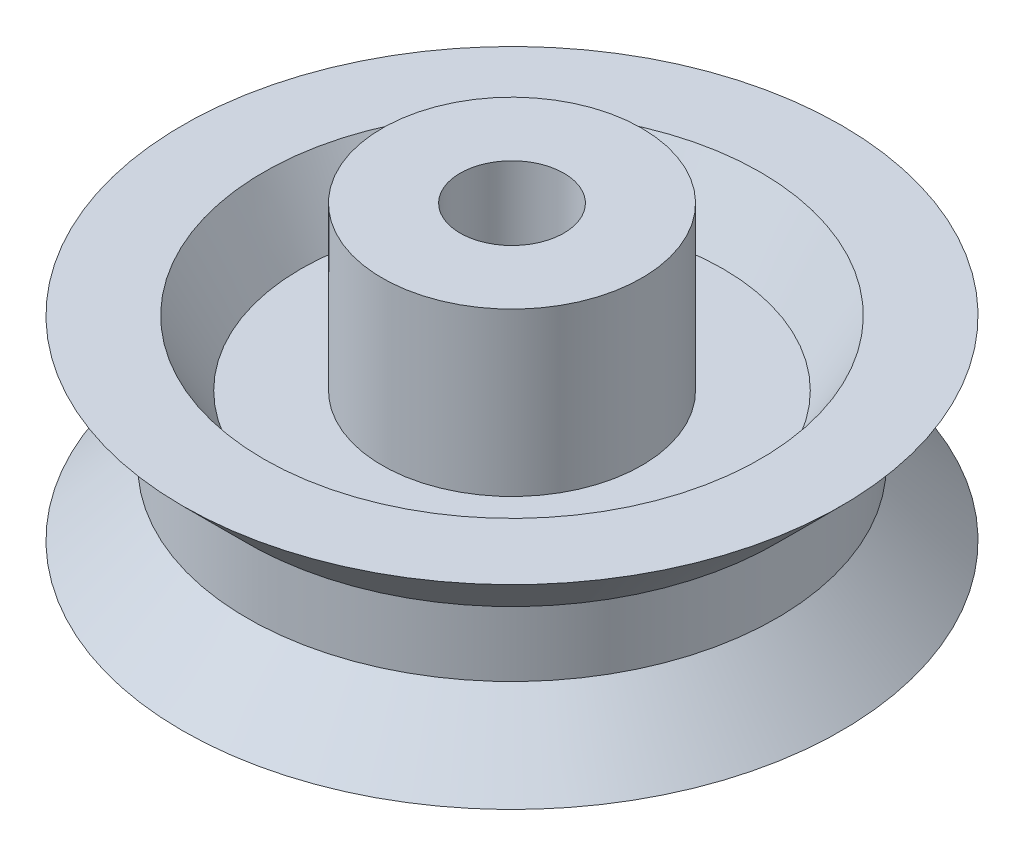
SolidWorks part; units mm, degrees
ref_plane "Plan de face" through (0, 0, 0) normal (0, 0, 1) x (1, 0, 0)
ref_plane "Plan de dessus" through (0, 0, 0) normal (0, 1, 0) x (1, 0, 0)
ref_plane "Plan de droite" through (0, 0, 0) normal (1, 0, 0) x (0, 0, -1)
sketch "Esquisse2" plane through (0, 0, 0) normal (1, 0, 0) x (0, 0, -1)
  line L0 (4, 0) -> (4, -5)
  line L1 (1.6, -5) -> (4, -5)
  line L2 (0, 0) -> (0, 15.5069) construction
  line L14 (4, 0) -> (6.5, 0)
  line L15 (6.5, 0) -> (7.6547, -2)
  line L16 (7.6547, -2) -> (10.1547, -2)
  line L17 (10.1547, -2) -> (8.1547, 0)
  line L18 (8.1547, 0) -> (8.1547, 2)
  line L19 (8.1547, 2) -> (10.1547, 4)
  line L20 (10.1547, 4) -> (7.6547, 4)
  line L21 (7.6547, 4) -> (6.5, 2)
  line L22 (6.5, 2) -> (4, 2)
  line L23 (4, 2) -> (4, 7)
  line L24 (4, 7) -> (1.6, 7)
  line L25 (1.6, 7) -> (1.6, -5)
  dimension "D1" = 135
  dimension "D2" = 135
  dimension "D3" = 120
  dimension "D4" = 120
  dimension "D5" = 2
  dimension "D6" = 2.5
  dimension "D7" = 2
  dimension "D8" = 5
  dimension "D9" = 2.5
  dimension "D10" = 2.4
  dimension "D11" = 1.6
  dimension "D12" = 5
  dimension "D13" = 2
  dimension "D14" = 12
  dimension "D15" = 2
  dimension "D16" = 2
  dimension "D17" = 2
  dimension "D18" = 5
revolve "Révolution1" add sketch "Esquisse2" angle 360 about L2
